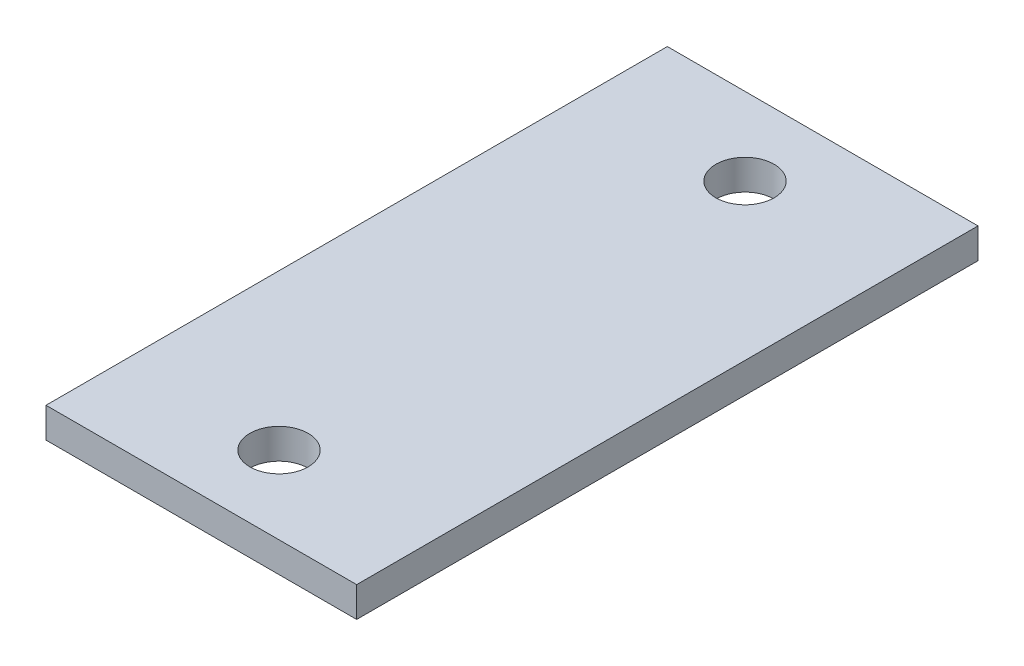
SolidWorks part; units mm, degrees
material "Plain Carbon Steel"
ref_plane "Front Plane" through (0, 0, 0) normal (0, 0, 1) x (1, 0, 0)
ref_plane "Top Plane" through (0, 0, 0) normal (0, 1, 0) x (1, 0, 0)
ref_plane "Right Plane" through (0, 0, 0) normal (1, 0, 0) x (0, 0, -1)
sketch "Sketch1" plane through (0, 0, 0) normal (0, 1, 0) x (1, 0, 0)
  line L1 (0, 0) -> (50.8, 0)
  line L2 (0, 0) -> (0, 101.6)
  line L3 (0, 101.6) -> (50.8, 101.6)
  line L4 (50.8, 0) -> (50.8, 101.6)
  line L8 (0, 12.7) -> (50.8, 12.7) construction
  circle A0 centre (25.4, 12.7) radius 4.7625
  circle A1 centre (25.4, 88.9) radius 4.7625
  dimension "D6" = 9.525
  dimension "D1" = 101.6
  dimension "D2" = 88.9
  dimension "D3" = 25.4
  dimension "D5" = 50.8
  dimension "D7" = 88.9
extrude "Hammer" add sketch "Sketch1" along normal blind 4.9352
